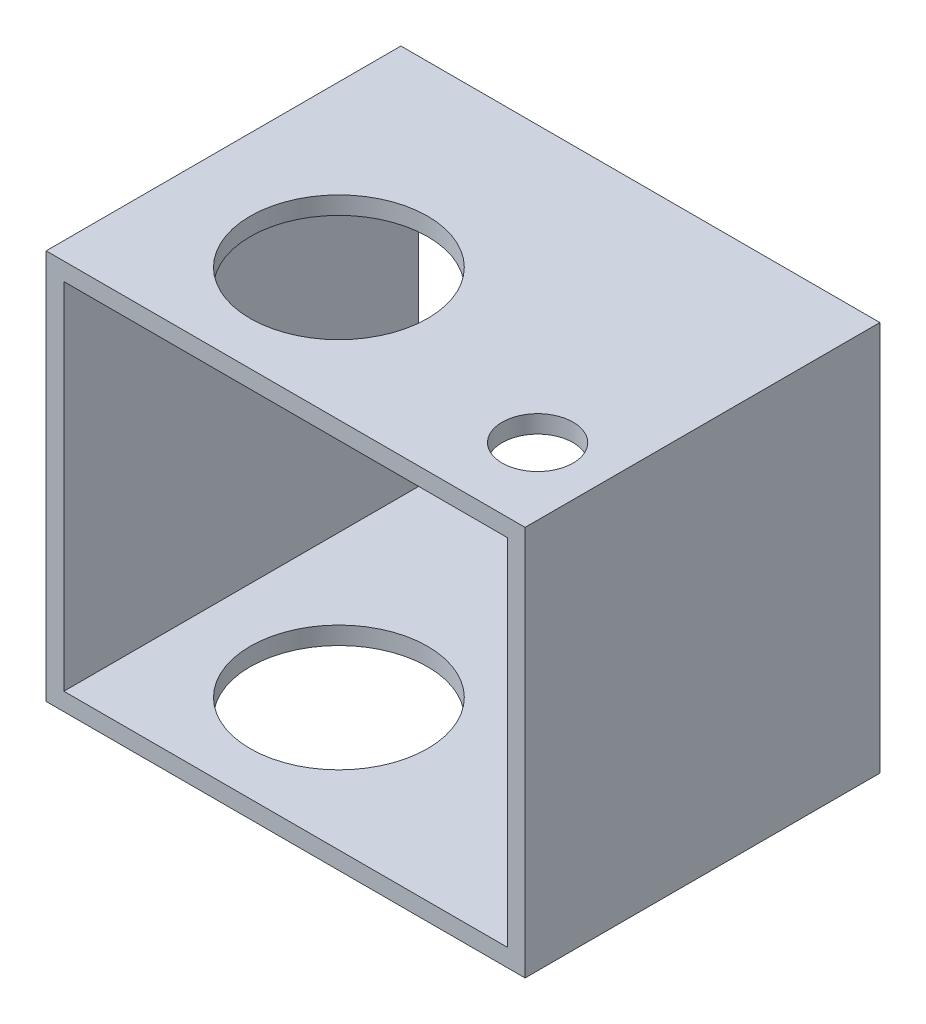
SolidWorks part; units mm, degrees
ref_plane "Plano frontal" through (0, 0, 0) normal (0, 0, 1) x (1, 0, 0)
ref_plane "Plano superior" through (0, 0, 0) normal (0, 1, 0) x (1, 0, 0)
ref_plane "Plano direito" through (0, 0, 0) normal (1, 0, 0) x (0, 0, -1)
sketch "Esboço1" plane through (0, 0, 0) normal (0, 0, 1) x (1, 0, 0)
  line L1 (0, 0) -> (-25, 0)
  line L2 (0, 0) -> (0, 20)
  line L3 (0, 20) -> (-25, 20)
  line L4 (-25, 0) -> (-25, 20)
extrude "Extrusão-Fina1" add sketch "Esboço1" along normal blind 20 thin thin type one direction wall 1
sketch "Esboço2" plane through (0, 21, 0) normal (0, 1, 0) x (1, 0, 0)
  circle A0 centre (-16.9444, -12.5518) radius 5
extrude "Corte-extrusão1" cut sketch "Esboço2" against normal through all
sketch "Esboço3" plane through (0, 21, 0) normal (0, 1, 0) x (1, 0, 0)
  circle A0 centre (-2.7849, -15.5087) radius 2
extrude "Corte-extrusão2" cut sketch "Esboço3" against normal blind 10
